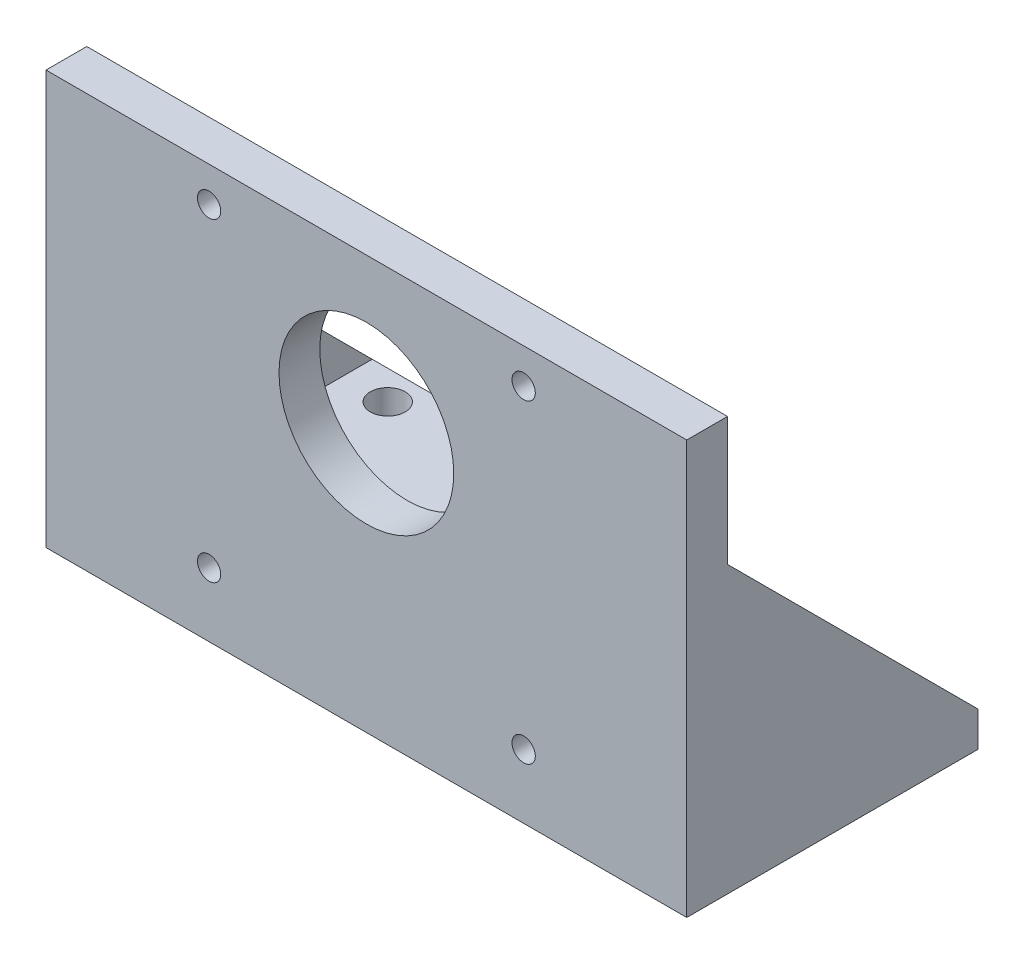
SolidWorks part; units mm, degrees
ref_plane "Front Plane" through (0, 0, 0) normal (0, 0, 1) x (1, 0, 0)
ref_plane "Top Plane" through (0, 0, 0) normal (0, 1, 0) x (1, 0, 0)
ref_plane "Right Plane" through (0, 0, 0) normal (1, 0, 0) x (0, 0, -1)
sketch "Sketch1" plane through (0, 0, 0) normal (0, 1, 0) x (1, 0, 0)
  line L0 (-55, 25) -> (55, -25) construction
  line L1 (-55, 25) -> (55, 25)
  line L2 (-55, 25) -> (-55, -25)
  line L3 (-55, -25) -> (55, -25)
  line L4 (55, 25) -> (55, -25)
  line L5 (-52.8831, 17.5) -> (53.0346, 17.5)
  circle A0 centre (0, 0) radius 17.5
  dimension "D1" = 110
  dimension "D2" = 50
  dimension "D3" = 7.5
extrude "Boss-Extrude1" add sketch "Sketch1" along normal blind 6
sketch "Sketch2" plane through (0, 6, 0) normal (0, 1, 0) x (1, 0, 0)
  line L0 (55, 25) -> (55, -25) construction
  line L1 (-55, -25) -> (55, -25)
  line L2 (-55, -25) -> (-55, -18)
  line L3 (-55, -18) -> (55, -18)
  line L4 (55, -25) -> (55, -18)
  dimension "D1" = 7
extrude "Boss-Extrude2" add sketch "Sketch2" along normal blind 65
ref_plane "Plane1" through (55, 0, 0) normal (1, 0, 0) x (0, 0, -1)
sketch "Sketch3" plane through (55, 0, 0) normal (1, 0, 0) x (0, 0, -1)
  line L0 (-18, 6) -> (25, 6)
  line L1 (-18, 6) -> (-18, 49)
  line L2 (-18, 71) -> (-18, 6) construction
  line L3 (-18, 49) -> (25, 6)
  dimension "D1" = 43
  dimension "D2" = 43
extrude "Boss-Extrude3" add sketch "Sketch3" against normal blind 6
ref_plane "Plane2" through (-55, 0, 0) normal (-1, 0, 0) x (0, 0, 1)
sketch "Sketch4" plane through (-55, 0, 0) normal (-1, 0, 0) x (0, 0, 1)
  line L0 (-25, 6) -> (18, 6)
  line L1 (18, 6) -> (18, 49)
  line L2 (18, 49) -> (-25, 6)
extrude "Boss-Extrude4" add sketch "Sketch4" against normal blind 6
sketch "Sketch5" plane through (0, 0, 25) normal (0, 0, 1) x (1, 0, 0)
  line L0 (0, 71) -> (0, 61) construction
  line L1 (-55, 71) -> (55, 71) construction
  line L2 (0, 61) -> (0, 46) construction
  circle A0 centre (0, 46) radius 15
  dimension "D1" = 10
extrude "Cut-Extrude1" cut sketch "Sketch5" against normal up to next
sketch "Sketch6" plane through (0, 6, 0) normal (0, 1, 0) x (1, 0, 0)
  line L0 (-41.3297, 20) -> (-41.3297, -13) construction
  line L1 (-49, 25) -> (49, 25) construction
  line L2 (49, -18) -> (-49, -18) construction
  line L3 (0, 31.7118) -> (0, -18.6313) construction
  line L4 (-41.3297, 20) -> (41.3297, 20) construction
  circle A0 centre (-41.3297, 20) radius 3
  circle A1 centre (-41.3297, -13) radius 3
  circle A2 centre (41.3297, -13) radius 3
  circle A3 centre (41.3297, 20) radius 3
  dimension "D3" = 33
  dimension "D1" = 5
  dimension "D2" = 5
  dimension "D4" = 82.6594
extrude "Cut-Extrude2" cut sketch "Sketch6" against normal through all
sketch "Sketch7" plane through (0, 0, 25) normal (0, 0, 1) x (1, 0, 0)
  line L0 (-55, 71) -> (55, 71) construction
  line L1 (-27, 11) -> (-27, 65) construction
  line L3 (27, 65) -> (27, 11) construction
  circle A0 centre (-27, 65) radius 2
  circle A1 centre (27, 65) radius 2
  circle A2 centre (-27, 11) radius 2
  circle A3 centre (27, 11) radius 2
  dimension "D2" = 6
  dimension "D1" = 6
  dimension "D3" = 54
  dimension "D4" = 54
  dimension "D5" = 54
extrude "Cut-Extrude3" cut sketch "Sketch7" against normal through all
